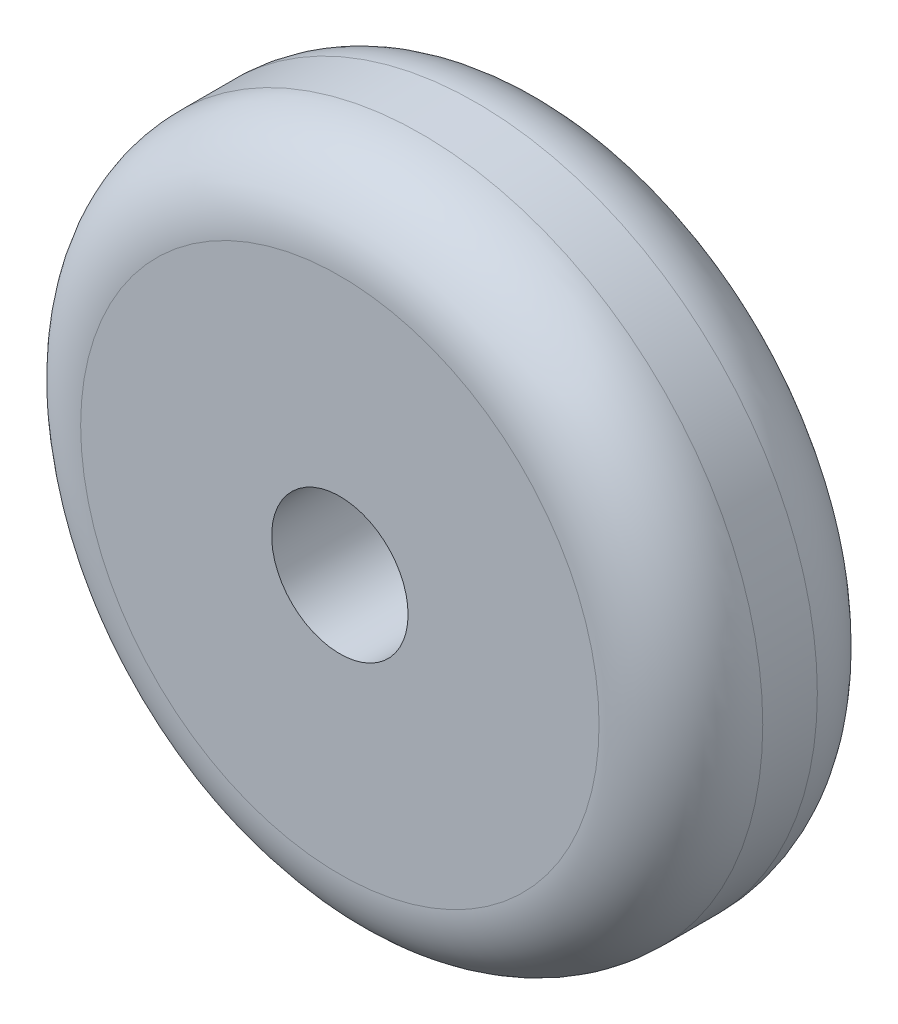
SolidWorks part; units mm, degrees
ref_plane "Front Plane" through (0, 0, 0) normal (0, 0, 1) x (1, 0, 0)
ref_plane "Top Plane" through (0, 0, 0) normal (0, 1, 0) x (1, 0, 0)
ref_plane "Right Plane" through (0, 0, 0) normal (1, 0, 0) x (0, 0, -1)
sketch "Sketch1" plane through (0, 0, 0) normal (0, 0, 1) x (1, 0, 0)
  circle A0 centre (0, 0) radius 12.5
  circle A1 centre (0, 0) radius 2.5
  dimension "D1" = 25
  dimension "D2" = 5
extrude "Boss-Extrude1" add sketch "Sketch1" along normal mid plane 8
fillet "Fillet1" radius 3 2 edges at (12.5, 0, -4) (12.5, 0, 4)
